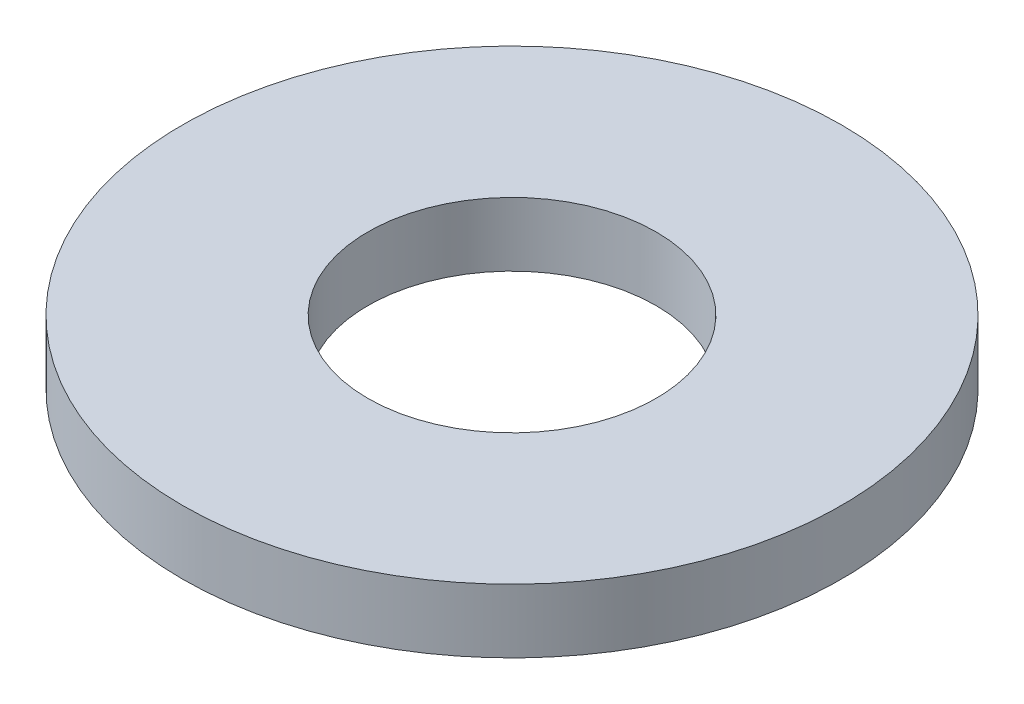
SolidWorks part; units mm, degrees
material "AISI 4130 Steel, annealed at 865C"
ref_plane "Front Plane" through (0, 0, 0) normal (0, 0, 1) x (1, 0, 0)
ref_plane "Top Plane" through (0, 0, 0) normal (0, 1, 0) x (1, 0, 0)
ref_plane "Right Plane" through (0, 0, 0) normal (1, 0, 0) x (0, 0, -1)
sketch "Sketch1" plane through (0, 0, 0) normal (0, 0, 1) x (1, 0, 0)
  line L0 (3.556, 0) -> (3.556, -1.5748)
  line L1 (3.556, -1.5748) -> (8.128, -1.5748)
  line L2 (8.128, -1.5748) -> (8.128, 0)
  line L3 (8.128, 0) -> (3.556, 0)
  line L4 (0, 0) -> (0, -1.5748) construction
  dimension "D1" = 3.556
  dimension "D2" = 8.128
  dimension "D3" = 1.5748
revolve "Revolve1" add sketch "Sketch1" angle 360 about L4
